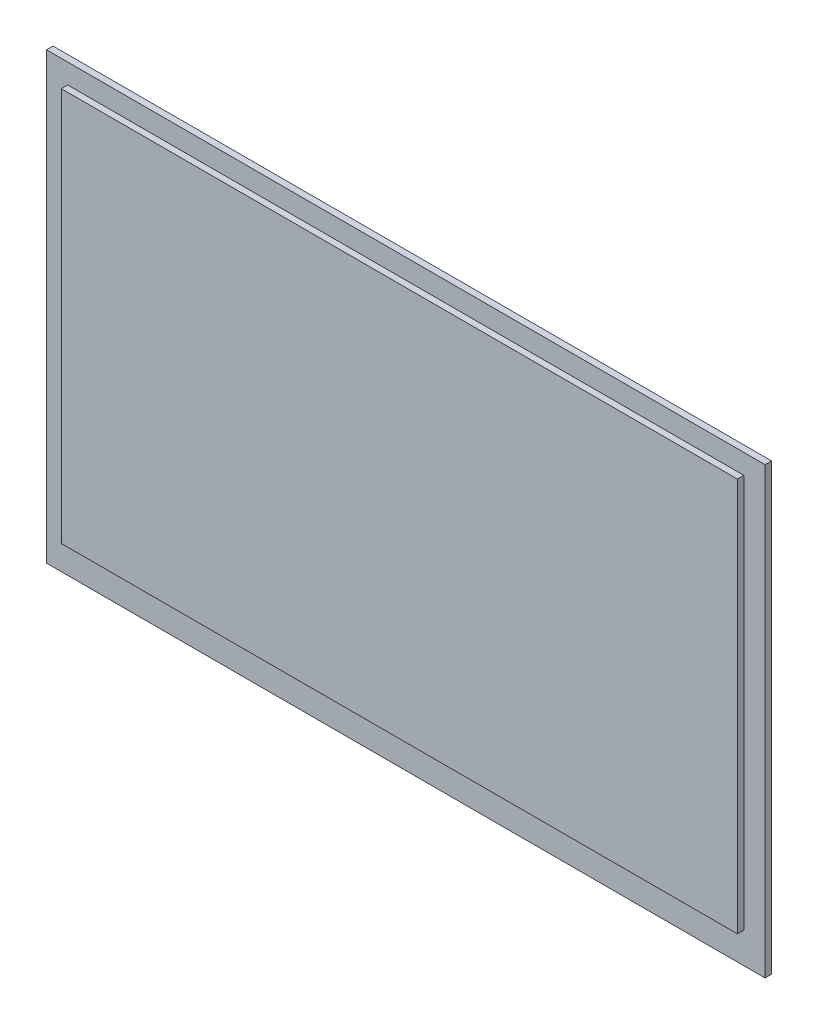
SolidWorks part; units mm, degrees
ref_plane "Front Plane" through (0, 0, 0) normal (0, 0, 1) x (1, 0, 0)
ref_plane "Top Plane" through (0, 0, 0) normal (0, 1, 0) x (1, 0, 0)
ref_plane "Right Plane" through (0, 0, 0) normal (1, 0, 0) x (0, 0, -1)
sketch "Sketch1" plane through (0, 0, 0) normal (0, 0, 1) x (1, 0, 0)
  line L1 (-52.45, -32.45) -> (52.45, -32.45)
  line L2 (-52.45, -32.45) -> (-52.45, 32.45)
  line L3 (-52.45, 32.45) -> (52.45, 32.45)
  line L4 (52.45, -32.45) -> (52.45, 32.45)
  line L5 (-52.45, -32.45) -> (52.45, 32.45) construction
  line L6 (-52.45, 32.45) -> (52.45, -32.45) construction
  point P0 (0, 0)
  dimension "D1" = 104.9
  dimension "D2" = 64.9
extrude "Boss-Extrude1" add sketch "Sketch1" along normal blind 0.95
sketch "Sketch2" plane through (0, 0, 0.95) normal (0, 0, 1) x (1, 0, 0)
  line L0 (-52.45, -32.45) -> (52.45, -32.45) construction
  line L1 (-49.35, -27.95) -> (49.35, -27.95)
  line L2 (-49.35, -27.95) -> (-49.35, 29.55)
  line L3 (-49.35, 29.55) -> (49.35, 29.55)
  line L4 (49.35, -27.95) -> (49.35, 29.55)
  line L5 (-49.35, -27.95) -> (49.35, 29.55) construction
  line L6 (-49.35, 29.55) -> (49.35, -27.95) construction
  point P0 (0, 0.8)
  dimension "D1" = 98.7
  dimension "D2" = 57.5
  dimension "D3" = 4.5
extrude "Boss-Extrude2" add sketch "Sketch2" along normal blind 0.935
